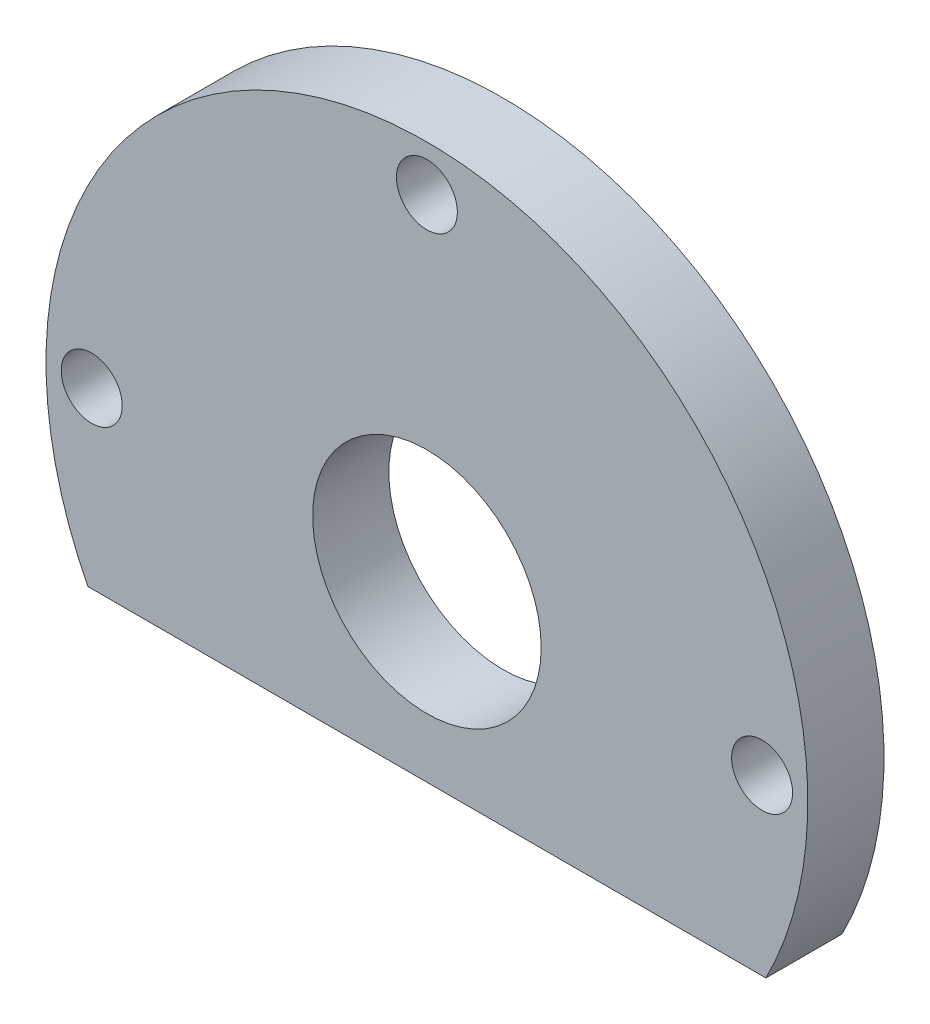
SolidWorks part; units mm, degrees
ref_plane "Front Plane" through (0, 0, 0) normal (0, 0, 1) x (1, 0, 0)
ref_plane "Top Plane" through (0, 0, 0) normal (0, 1, 0) x (1, 0, 0)
ref_plane "Right Plane" through (0, 0, 0) normal (1, 0, 0) x (0, 0, -1)
sketch "Sketch1" plane through (0, 0, 0) normal (0, 0, 1) x (1, 0, 0)
  circle A0 centre (0, 0) radius 7.5
  circle A1 centre (0, 0) radius 25
  dimension "D1" = 15
  dimension "D2" = 50
extrude "Boss-Extrude1" add sketch "Sketch1" along normal blind 5
sketch "Sketch2" plane through (0, 0, 5) normal (0, 0, 1) x (1, 0, 0)
  line L0 (0, 22) -> (0, 0) construction
  line L1 (0, 0) -> (-22, 0) construction
  line L2 (0, 0) -> (22, 0) construction
  line L3 (-22.2497, -11.3996) -> (22.2497, -11.3996)
  circle A1 centre (0, 22) radius 2
  circle A2 centre (22, 0) radius 2
  circle A3 centre (-22, 0) radius 2
  circle A4 centre (0, 0) radius 25 construction
  arc A6 (-22.2497, -11.3996) -> (22.2497, -11.3996) centre (0, 0) ccw
  dimension "D1" = 22
  dimension "D2" = 4
  dimension "D3" = 11.3996
extrude "Cut-Extrude1" cut sketch "Sketch2" against normal blind 5
sketch "Sketch3" plane through (0, 0, 5) normal (0, 0, 1) x (1, 0, 0)
  circle A0 centre (0, 0) radius 7.5
  circle A1 centre (0, 0) radius 10
  dimension "D1" = 20
